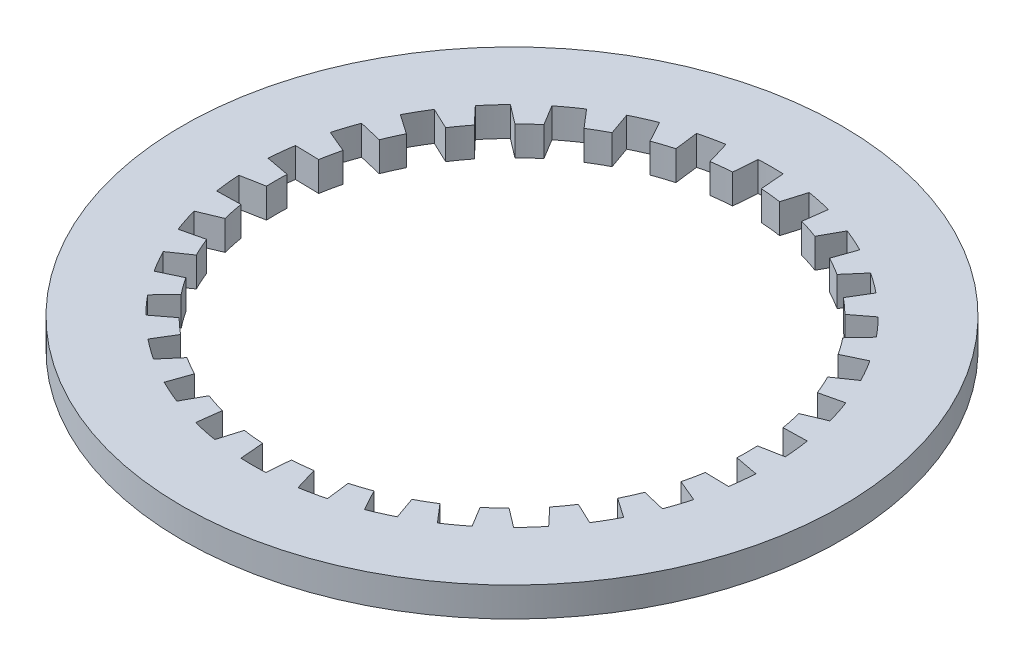
SolidWorks part; units mm, degrees
ref_plane "Front Plane" through (0, 0, 0) normal (0, 0, 1) x (1, 0, 0)
ref_plane "Top Plane" through (0, 0, 0) normal (0, 1, 0) x (1, 0, 0)
ref_plane "Right Plane" through (0, 0, 0) normal (1, 0, 0) x (0, 0, -1)
sketch "Sketch1" plane through (0, 0, 0) normal (0, 1, 0) x (1, 0, 0)
  circle A0 centre (0, 0) radius 17.78
extrude "Boss-Extrude1" add sketch "Sketch1" along normal blind 1.5875
sketch "Sketch2" plane through (0, 1.5875, 0) normal (0, 1, 0) x (1, 0, 0)
  line L1 (-0.6703, 13.9539) -> (-0.7753, 12.6763)
  line L2 (0.6703, 13.9539) -> (0.7753, 12.6763)
  line L3 (2.2456, 13.7883) -> (1.8772, 12.5605)
  line L4 (3.5568, 13.5096) -> (3.3939, 12.2381)
  line L5 (5.0633, 13.0201) -> (4.4476, 11.8957)
  line L6 (6.2879, 12.4749) -> (5.8642, 11.265)
  line L7 (7.6597, 11.6829) -> (6.8237, 10.7111)
  line L8 (8.7442, 10.895) -> (8.0782, 9.7996)
  line L9 (9.9213, 9.8351) -> (8.9015, 9.0583)
  line L10 (10.8183, 8.8389) -> (9.9391, 7.9059)
  line L11 (11.7493, 7.5574) -> (10.5903, 7.0096)
  line L12 (12.4196, 6.3965) -> (11.3657, 5.6667)
  line L13 (13.0638, 4.9494) -> (11.8163, 4.6546)
  line L14 (13.4781, 3.6745) -> (12.2955, 3.1798)
  line L15 (13.8074, 2.1252) -> (12.5258, 2.0961)
  line L16 (13.9475, 0.792) -> (12.6879, 0.554)
  line L17 (13.9475, -0.792) -> (12.6879, -0.554)
  line L18 (13.8074, -2.1252) -> (12.5258, -2.0961)
  line L19 (13.4781, -3.6745) -> (12.2955, -3.1798)
  line L20 (13.0638, -4.9494) -> (11.8163, -4.6546)
  line L21 (12.4196, -6.3965) -> (11.3657, -5.6667)
  line L22 (11.7493, -7.5574) -> (10.5903, -7.0096)
  line L23 (10.8183, -8.8389) -> (9.9391, -7.9059)
  line L24 (9.9213, -9.8351) -> (8.9015, -9.0583)
  line L25 (8.7442, -10.895) -> (8.0782, -9.7996)
  line L26 (7.6597, -11.6829) -> (6.8237, -10.7111)
  line L27 (6.2879, -12.4749) -> (5.8642, -11.265)
  line L28 (5.0633, -13.0201) -> (4.4476, -11.8957)
  line L29 (3.5568, -13.5096) -> (3.3939, -12.2381)
  line L30 (2.2456, -13.7883) -> (1.8772, -12.5605)
  line L31 (0.6703, -13.9539) -> (0.7753, -12.6763)
  line L32 (-0.6703, -13.9539) -> (-0.7753, -12.6763)
  line L33 (-2.2456, -13.7883) -> (-1.8772, -12.5605)
  line L34 (-3.5568, -13.5096) -> (-3.3939, -12.2381)
  line L35 (-5.0633, -13.0201) -> (-4.4476, -11.8957)
  line L36 (-6.2879, -12.4749) -> (-5.8642, -11.265)
  line L37 (-7.6597, -11.6829) -> (-6.8237, -10.7111)
  line L38 (-8.7442, -10.895) -> (-8.0782, -9.7996)
  line L39 (-9.9213, -9.8351) -> (-8.9015, -9.0583)
  line L40 (-10.8183, -8.8389) -> (-9.9391, -7.9059)
  line L41 (-11.7493, -7.5574) -> (-10.5903, -7.0096)
  line L42 (-12.4196, -6.3965) -> (-11.3657, -5.6667)
  line L43 (-13.0638, -4.9494) -> (-11.8163, -4.6546)
  line L44 (-13.4781, -3.6745) -> (-12.2955, -3.1798)
  line L45 (-13.8074, -2.1252) -> (-12.5258, -2.0961)
  line L46 (-13.9475, -0.792) -> (-12.6879, -0.554)
  line L47 (-13.9475, 0.792) -> (-12.6879, 0.554)
  line L48 (-13.8074, 2.1252) -> (-12.5258, 2.0961)
  line L49 (-13.4781, 3.6745) -> (-12.2955, 3.1798)
  line L50 (-13.0638, 4.9494) -> (-11.8163, 4.6546)
  line L51 (-12.4196, 6.3965) -> (-11.3657, 5.6667)
  line L52 (-11.7493, 7.5574) -> (-10.5903, 7.0096)
  line L53 (-10.8183, 8.8389) -> (-9.9391, 7.9059)
  line L54 (-9.9213, 9.8351) -> (-8.9015, 9.0583)
  line L55 (-8.7442, 10.895) -> (-8.0782, 9.7996)
  line L56 (-7.6597, 11.6829) -> (-6.8237, 10.7111)
  line L57 (-6.2879, 12.4749) -> (-5.8642, 11.265)
  line L58 (-5.0633, 13.0201) -> (-4.4476, 11.8957)
  line L59 (-3.5568, 13.5096) -> (-3.3939, 12.2381)
  line L60 (-2.2456, 13.7883) -> (-1.8772, 12.5605)
  arc A0 (-2.2456, 13.7883) -> (-3.5568, 13.5096) centre (0, 0) ccw
  arc A1 (-0.7753, 12.6763) -> (-1.8772, 12.5605) centre (0, 0) ccw
  arc A2 (10.8183, 8.8389) -> (9.9213, 9.8351) centre (0, 0) ccw
  arc A3 (-7.6597, 11.6829) -> (-8.7442, 10.895) centre (0, 0) ccw
  arc A4 (-5.0633, 13.0201) -> (-6.2879, 12.4749) centre (0, 0) ccw
  arc A5 (0.6703, 13.9539) -> (-0.6703, 13.9539) centre (0, 0) ccw
  arc A6 (3.5568, 13.5096) -> (2.2456, 13.7883) centre (0, 0) ccw
  arc A7 (6.2879, 12.4749) -> (5.0633, 13.0201) centre (0, 0) ccw
  arc A8 (8.7442, 10.895) -> (7.6597, 11.6829) centre (0, 0) ccw
  arc A9 (-9.9213, 9.8351) -> (-10.8183, 8.8389) centre (0, 0) ccw
  arc A10 (-11.7493, 7.5574) -> (-12.4196, 6.3965) centre (0, 0) ccw
  arc A11 (-13.0638, 4.9494) -> (-13.4781, 3.6745) centre (0, 0) ccw
  arc A12 (-11.3657, 5.6667) -> (-11.8163, 4.6546) centre (0, 0) ccw
  arc A13 (-9.9391, 7.9059) -> (-10.5903, 7.0096) centre (0, 0) ccw
  arc A14 (-8.0782, 9.7996) -> (-8.9015, 9.0583) centre (0, 0) ccw
  arc A15 (-5.8642, 11.265) -> (-6.8237, 10.7111) centre (0, 0) ccw
  arc A16 (-3.3939, 12.2381) -> (-4.4476, 11.8957) centre (0, 0) ccw
  arc A17 (1.8772, 12.5605) -> (0.7753, 12.6763) centre (0, 0) ccw
  arc A18 (4.4476, 11.8957) -> (3.3939, 12.2381) centre (0, 0) ccw
  arc A19 (6.8237, 10.7111) -> (5.8642, 11.265) centre (0, 0) ccw
  arc A20 (8.9015, 9.0583) -> (8.0782, 9.7996) centre (0, 0) ccw
  arc A21 (10.5903, 7.0096) -> (9.9391, 7.9059) centre (0, 0) ccw
  arc A22 (12.4196, 6.3965) -> (11.7493, 7.5574) centre (0, 0) ccw
  arc A23 (11.8163, 4.6546) -> (11.3657, 5.6667) centre (0, 0) ccw
  arc A24 (-12.2955, 3.1798) -> (-12.5258, 2.0961) centre (0, 0) ccw
  arc A25 (-13.8074, 2.1252) -> (-13.9475, 0.792) centre (0, 0) ccw
  arc A26 (-12.6879, 0.554) -> (-12.6879, -0.554) centre (0, 0) ccw
  arc A27 (-13.9475, -0.792) -> (-13.8074, -2.1252) centre (0, 0) ccw
  arc A28 (-12.5258, -2.0961) -> (-12.2955, -3.1798) centre (0, 0) ccw
  arc A29 (-13.4781, -3.6745) -> (-13.0638, -4.9494) centre (0, 0) ccw
  arc A30 (-11.8163, -4.6546) -> (-11.3657, -5.6667) centre (0, 0) ccw
  arc A31 (-12.4196, -6.3965) -> (-11.7493, -7.5574) centre (0, 0) ccw
  arc A32 (-10.5903, -7.0096) -> (-9.9391, -7.9059) centre (0, 0) ccw
  arc A33 (-10.8183, -8.8389) -> (-9.9213, -9.8351) centre (0, 0) ccw
  arc A34 (-8.9015, -9.0583) -> (-8.0782, -9.7996) centre (0, 0) ccw
  arc A35 (-8.7442, -10.895) -> (-7.6597, -11.6829) centre (0, 0) ccw
  arc A36 (-6.8237, -10.7111) -> (-5.8642, -11.265) centre (0, 0) ccw
  arc A37 (-6.2879, -12.4749) -> (-5.0633, -13.0201) centre (0, 0) ccw
  arc A38 (-4.4476, -11.8957) -> (-3.3939, -12.2381) centre (0, 0) ccw
  arc A39 (-3.5568, -13.5096) -> (-2.2456, -13.7883) centre (0, 0) ccw
  arc A40 (-1.8772, -12.5605) -> (-0.7753, -12.6763) centre (0, 0) ccw
  arc A41 (-0.6703, -13.9539) -> (0.6703, -13.9539) centre (0, 0) ccw
  arc A42 (0.7753, -12.6763) -> (1.8772, -12.5605) centre (0, 0) ccw
  arc A43 (2.2456, -13.7883) -> (3.5568, -13.5096) centre (0, 0) ccw
  arc A44 (3.3939, -12.2381) -> (4.4476, -11.8957) centre (0, 0) ccw
  arc A45 (5.0633, -13.0201) -> (6.2879, -12.4749) centre (0, 0) ccw
  arc A46 (5.8642, -11.265) -> (6.8237, -10.7111) centre (0, 0) ccw
  arc A47 (7.6597, -11.6829) -> (8.7442, -10.895) centre (0, 0) ccw
  arc A48 (8.0782, -9.7996) -> (8.9015, -9.0583) centre (0, 0) ccw
  arc A49 (9.9213, -9.8351) -> (10.8183, -8.8389) centre (0, 0) ccw
  arc A50 (9.9391, -7.9059) -> (10.5903, -7.0096) centre (0, 0) ccw
  arc A51 (11.7493, -7.5574) -> (12.4196, -6.3965) centre (0, 0) ccw
  arc A52 (11.3657, -5.6667) -> (11.8163, -4.6546) centre (0, 0) ccw
  arc A53 (13.0638, -4.9494) -> (13.4781, -3.6745) centre (0, 0) ccw
  arc A54 (12.2955, -3.1798) -> (12.5258, -2.0961) centre (0, 0) ccw
  arc A55 (13.8074, -2.1252) -> (13.9475, -0.792) centre (0, 0) ccw
  arc A56 (12.6879, -0.554) -> (12.6879, 0.554) centre (0, 0) ccw
  arc A57 (13.9475, 0.792) -> (13.8074, 2.1252) centre (0, 0) ccw
  arc A58 (12.5258, 2.0961) -> (12.2955, 3.1798) centre (0, 0) ccw
  arc A59 (13.4781, 3.6745) -> (13.0638, 4.9494) centre (0, 0) ccw
  point P130 (0, 0)
  dimension "D1" = 30
extrude "Cut-Extrude1" cut sketch "Sketch2" against normal through all contours A13 L52 A10 L51 A12 L50 A11 L49 A24 L48 A25 L47 A26 L46 A27 L45 A28 L44 A29 L43 A30 L42 A31 L41 A32 L40 A33 L39 A34 L38 A35 L37 A36 L36 A37 L35 A38 L34 A39 L33 A40 L32 A41 L31 A42 L30 A43 L29 A44 L28 A45 L27 A46 L26 A47 L25 A48 L24 A49 L23 A50 L22 A51 L21 A52 L20 A53 L19 A54 L18 A55 L17 A56 L16 A57 L15 A58 L14 A59 L13 A23 L12 A22 L11 A21 L10 A2 L9 A20 L8 A8 L7 A19 L6 A7 L5 A18 L4 A6 L3 A17 L2 A5 L1 A1 L60 A0 L59 A16 L58 A4 L57 A15 L56 A3 L55 A14 L54 A9 L53
